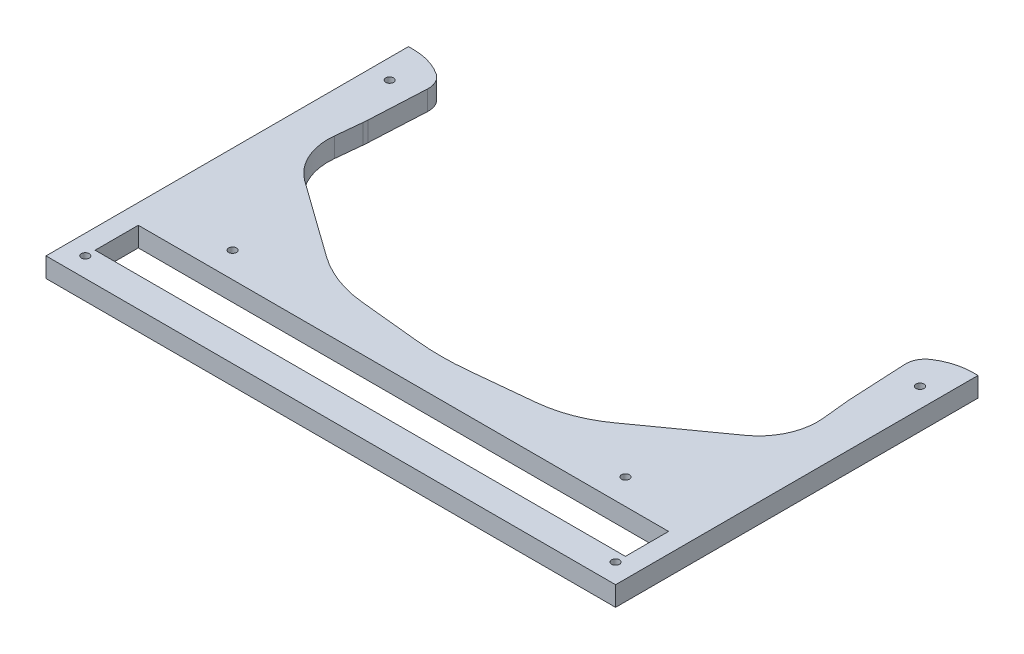
SolidWorks part; units mm, degrees
material "Acrylique (impact moyen-haut)"
ref_plane "Plan de face" through (0, 0, 0) normal (0, 0, 1) x (1, 0, 0)
ref_plane "Plan de dessus" through (0, 0, 0) normal (0, 1, 0) x (1, 0, 0)
ref_plane "Plan de droite" through (0, 0, 0) normal (1, 0, 0) x (0, 0, -1)
sketch "Esquisse2" plane through (0, 0, 0) normal (0, 1, 0) x (1, 0, 0)
  line L0 (145, 290) -> (145, 0) construction
  line L1 (0, 0) -> (290, 0)
  line L2 (0, 0) -> (0, 184.53)
  line L4 (290, 0) -> (290, 184.53)
  line L6 (0, 184.53) -> (2.5736, 184.53)
  line L7 (23.7868, 175.7432) -> (109.53, 90)
  line L8 (109.53, 90) -> (180.47, 90)
  line L9 (290, 184.53) -> (287.4264, 184.53)
  line L10 (266.2132, 175.7432) -> (180.47, 90)
  arc A0 (2.5736, 184.53) -> (23.7868, 175.7432) centre (2.5736, 154.53) cw
  arc A1 (287.4264, 184.53) -> (266.2132, 175.7432) centre (287.4264, 154.53) ccw
  point P7 (15, 184.53)
  point P16 (145, 90)
  point P17 (275, 184.53)
  dimension "D1" = 30
  dimension "D7" = 30
  dimension "D2" = 290
  dimension "D3" = 15
  dimension "D4" = 94.53
  dimension "D5" = 90
  dimension "D6" = 135
extrude "Boss.-Extru.1" add sketch "Esquisse2" along normal blind 10
sketch "Esquisse3" plane through (0, 10, 0) normal (0, 1, 0) x (1, 0, 0)
  line L0 (0, 92.265) -> (290, 92.265) construction
  line L1 (0, 184.53) -> (0, 0) construction
  line L2 (290, 0) -> (290, 184.53) construction
  line L3 (145, 290) -> (145, 0) construction
  line L5 (0, 0) -> (290, 0) construction
  line L6 (0, 184.53) -> (0, 0) construction
  circle A0 centre (10, 10) radius 2
  circle A1 centre (280, 10) radius 2
  dimension "D3" = 10
  dimension "D1" = 4
  dimension "D2" = 10
extrude "Enlèv. mat.-Extru.1" cut sketch "Esquisse3" against normal blind 10
sketch "Esquisse6" plane through (0, 10, 0) normal (0, 1, 0) x (1, 0, 0)
  line L0 (145, 15) -> (145, 0) construction
  line L1 (10, 37) -> (280, 37)
  line L2 (10, 37) -> (10, 15)
  line L3 (10, 15) -> (280, 15)
  line L4 (280, 37) -> (280, 15)
  line L5 (0, 0) -> (290, 0) construction
  circle A0 centre (280, 10) radius 2 construction
  dimension "D3" = 5
  dimension "D1" = 22
  dimension "D2" = 270
extrude "Enlèv. mat.-Extru.4" cut sketch "Esquisse6" against normal blind 10
sketch "Esquisse9" plane through (0, 10, 0) normal (0, 1, 0) x (1, 0, 0)
  line L0 (145, 0) -> (145, 146.3019) construction
  line L1 (0, 0) -> (290, 0) construction
  line L2 (0, 184.53) -> (0, 0) construction
  circle A0 centre (45, 50) radius 2
  circle A1 centre (245, 50) radius 2
  dimension "D1" = 4
  dimension "D2" = 45
  dimension "D3" = 50
extrude "Enlèv. mat.-Extru.7" cut sketch "Esquisse9" against normal blind 10
sketch "Esquisse11" plane through (0, 0, 0) normal (0, -1, 0) x (1, 0, 0)
  line L0 (145, -37) -> (145, -167.6677) construction
  line L1 (10, -37) -> (280, -37) construction
  line L2 (23.7868, -175.7432) -> (22.0693, -141.9696)
  line L3 (12.1557, -135.0962) -> (47.7545, -155.4364) construction
  line L4 (21.8806, -139.4838) -> (20.543, -126.2423)
  line L5 (32.9315, -98.8313) -> (71.775, -71.0318)
  line L6 (100.664, -60.1274) -> (131.9344, -56.9686)
  line L7 (266.2132, -175.7432) -> (267.9307, -141.9696)
  line L8 (268.1194, -139.4838) -> (269.457, -126.2423)
  line L9 (257.0685, -98.8313) -> (218.225, -71.0318)
  line L10 (189.336, -60.1274) -> (158.0656, -56.9686)
  line L11 (23.7868, -175.7432) -> (266.2132, -175.7432)
  circle A0 centre (50.3097, -116.8937) radius 32.5 construction
  circle A1 centre (110.0489, -82.1564) radius 32.5 construction
  arc A2 (22.0693, -141.9696) -> (21.8806, -139.4838) centre (-27.8662, -144.509) ccw
  arc A3 (20.543, -126.2423) -> (32.9315, -98.8313) centre (50.3911, -123.2272) cw
  arc A4 (71.775, -71.0318) -> (100.664, -60.1274) centre (106.6943, -119.8236) cw
  arc A5 (267.9307, -141.9696) -> (268.1194, -139.4838) centre (317.8662, -144.509) cw
  arc A6 (269.457, -126.2423) -> (257.0685, -98.8313) centre (239.6089, -123.2272) ccw
  arc A7 (218.225, -71.0318) -> (189.336, -60.1274) centre (183.3057, -119.8236) ccw
  arc A8 (131.9344, -56.9686) -> (158.0656, -56.9686) centre (145, -186.3104) cw
  point P18 (17.8097, -116.8937)
  point P19 (22.0059, -140.7244)
  point P22 (18.796, -108.9478)
  point P25 (84.7676, -61.7332)
  point P38 (145, -55.6488)
  dimension "D1" = 50
  dimension "D2" = 30
  dimension "D3" = 60
  dimension "D4" = 130
extrude "Enlèv. mat.-Extru.9" cut sketch "Esquisse11" along direction (0, -1, 0) on the side against the normal blind 10
fillet "Congé5" radius 10 2 edges at (266.2132, 5, -175.7432) (23.7868, 5, -175.7432)
sketch "Esquisse12" plane through (0, 0, 0) normal (0, -1, 0) x (1, 0, 0)
  circle A0 centre (10, -165) radius 2
  circle A1 centre (280, -165) radius 2
extrude "Enlèv. mat.-Extru.10" cut sketch "Esquisse12" against normal blind 10
sketch "Esquisse14" plane through (0, 0, 0) normal (0, -1, 0) x (1, 0, 0)
  circle A0 centre (10, -10) radius 6
  circle A1 centre (45, -50) radius 6
  circle A2 centre (10, -165) radius 6
  circle A3 centre (280, -165) radius 6
  circle A4 centre (245, -50) radius 6
  circle A5 centre (280, -10) radius 6
  dimension "D1" = 12
extrude "Enlèv. mat.-Extru.11" cut sketch "Esquisse14" against normal blind 5
